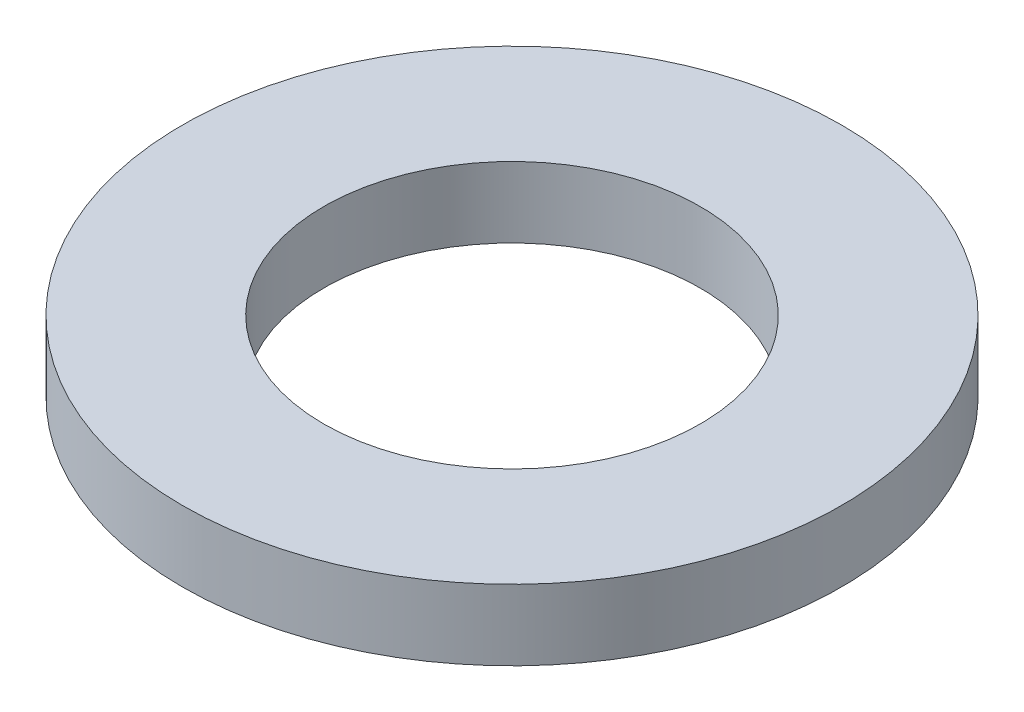
SolidWorks part; units mm, degrees
ref_plane "Alzado" through (0, 0, 0) normal (0, 0, 1) x (1, 0, 0)
ref_plane "Planta" through (0, 0, 0) normal (0, 1, 0) x (1, 0, 0)
ref_plane "Vista lateral" through (0, 0, 0) normal (1, 0, 0) x (0, 0, -1)
sketch "Croquis1" plane through (0, 0, 0) normal (0, 1, 0) x (1, 0, 0)
  circle A0 centre (0, 0) radius 8
  circle A1 centre (0, 0) radius 14
  dimension "D1" = 16
  dimension "D2" = 28
extrude "Saliente-Extruir1" add sketch "Croquis1" along normal blind 3
